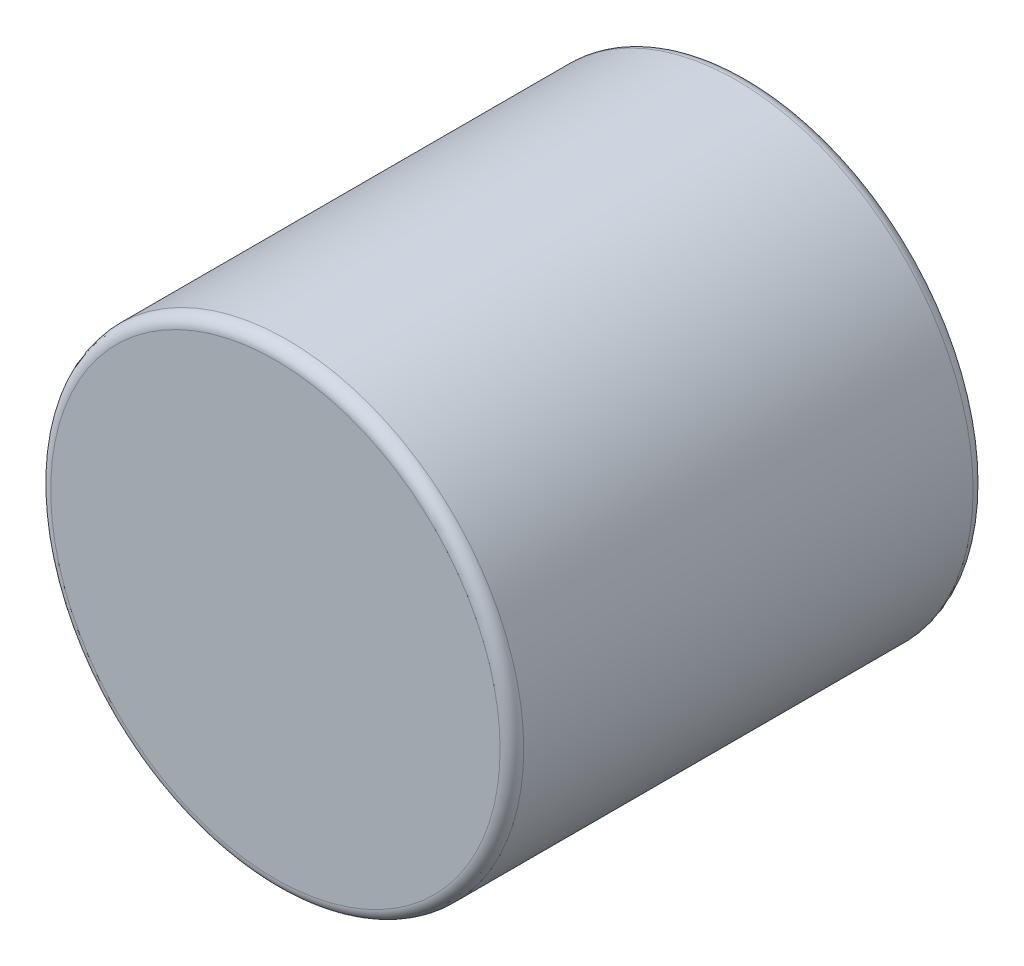
SolidWorks part; units mm, degrees
ref_plane "Front Plane" through (0, 0, 0) normal (0, 0, 1) x (1, 0, 0)
ref_plane "Top Plane" through (0, 0, 0) normal (0, 1, 0) x (1, 0, 0)
ref_plane "Right Plane" through (0, 0, 0) normal (1, 0, 0) x (0, 0, -1)
sketch "Sketch1" plane through (0, 0, 0) normal (0, 0, 1) x (1, 0, 0)
  circle A0 centre (0, 0) radius 0.7937 construction
  dimension "OD" = 1.5875
sketch "Sketch2" plane through (0, 0, 0) normal (1, 0, 0) x (0, 0, -1)
  line L0 (-0.7937, 0) -> (0.7937, 0) construction
  line L1 (0, 0.7937) -> (0, -0.7937) construction
  line L3 (-0.7937, 0.7937) -> (0.7938, 0.7938)
  line L4 (-0.7937, 0.7937) -> (-0.7937, -0.7937)
  line L5 (-0.7937, -0.7937) -> (0.7938, -0.7938)
  line L6 (0.7938, 0.7938) -> (0.7938, -0.7938)
  point P4 (0, 0)
  point P12 (0, 0.7937)
  dimension "Thickness" = 1.5875
sketch "Sketch3" plane through (0, 0, 0) normal (0, 0, 1) x (1, 0, 0)
  circle A0 centre (0, 0) radius 0.7937 construction
  circle A1 centre (0, 0) radius 0.7937
extrude "Boss-Extrude1" add sketch "Sketch3" along normal up to vertex (0.7937 mm away) and the other way up to vertex (0.7937 mm away) up to point (0, 0.7937, 0.7937) other way up to point (0, 0.7938, -0.7938)
fillet "Fillet1" radius 0.0397 2 edges at (0.7937, 0, -0.7938) (0.7937, 0, 0.7937)
equation "\"Fillet@Fillet1\"=\"Thickness@Sketch2\"*.025"
